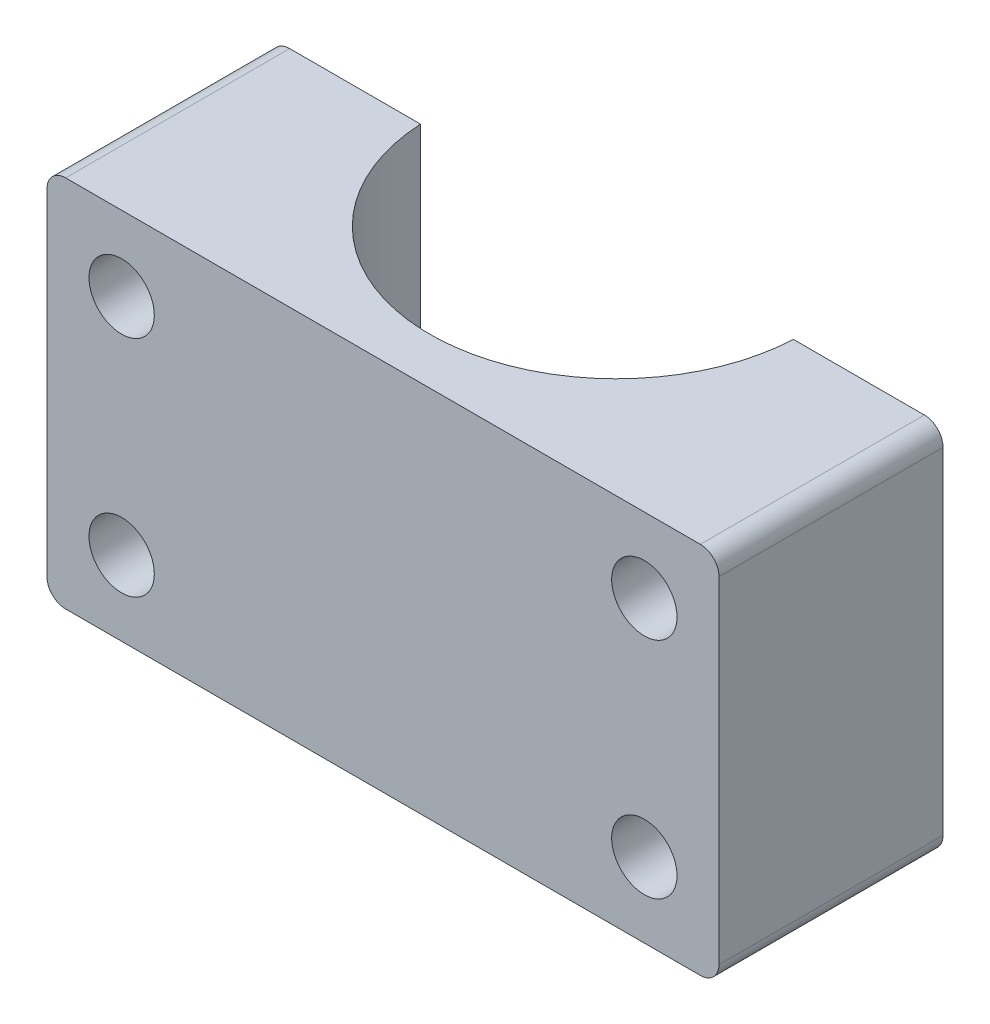
SolidWorks part; units mm, degrees
material "ABS"
ref_plane "Front Plane" through (0, 0, 0) normal (0, 0, 1) x (1, 0, 0)
ref_plane "Top Plane" through (0, 0, 0) normal (0, 1, 0) x (1, 0, 0)
ref_plane "Right Plane" through (0, 0, 0) normal (1, 0, 0) x (0, 0, -1)
sketch "Sketch1" plane through (0, 0, 0) normal (0, 1, 0) x (1, 0, 0)
  line L0 (-18, 0) -> (-18, -12)
  line L1 (-18, -12) -> (18, -12)
  line L2 (18, -12) -> (18, 0)
  line L3 (-9.9875, 0) -> (-18, 0)
  line L4 (9.9875, 0) -> (18, 0)
  arc A0 (-9.9875, 0) -> (9.9875, 0) centre (0, 0.5) ccw
  dimension "D1" = 10
  dimension "D2" = 36
  dimension "D3" = 0.5
  dimension "D4" = 12
extrude "Boss-Extrude1" add sketch "Sketch1" along normal blind 20
sketch "Sketch2" plane through (0, 0, 12) normal (0, 0, 1) x (1, 0, 0)
  line L0 (0, 10) -> (4.0591, 10) construction
  line L1 (-14, 16) -> (14, 16) construction
  line L2 (-14, 16) -> (-14, 4) construction
  line L3 (-14, 4) -> (14, 4) construction
  line L4 (14, 16) -> (14, 4) construction
  line L5 (-14, 16) -> (14, 4) construction
  line L6 (-14, 4) -> (14, 16) construction
  line L7 (-18, 0) -> (18, 0) construction
  line L8 (-18, 20) -> (18, 20) construction
  circle A0 centre (-14, 16) radius 1.75
  circle A1 centre (-14, 4) radius 1.75
  circle A2 centre (14, 4) radius 1.75
  circle A3 centre (14, 16) radius 1.75
  point P0 (0, 10)
  dimension "D3" = 3.5
  dimension "D1" = 28
  dimension "D2" = 12
extrude "Cut-Extrude1" cut sketch "Sketch2" against normal through all
fillet "Fillet1" radius 1 4 edges at (-18, 0, 6) (18, 0, 6) (-18, 20, 6) (18, 20, 6)
sketch "Sketch3" plane through (0, 0, 12) normal (0, 0, 1) x (1, 0, 0)
  circle A0 centre (-14, 16) radius 3
  circle A1 centre (-14, 4) radius 3
  circle A2 centre (14, 4) radius 3
  circle A3 centre (14, 16) radius 3
  dimension "D1" = 6
